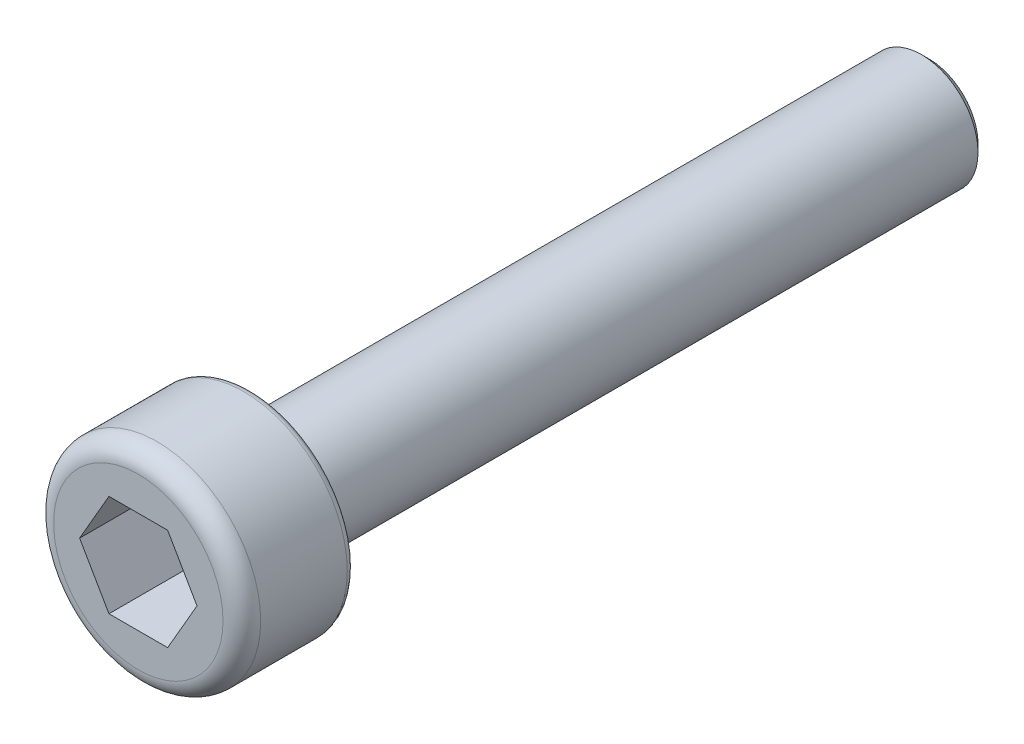
SolidWorks part; units mm, degrees
ref_plane "前视" through (0, 0, 0) normal (0, 0, 1) x (1, 0, 0)
ref_plane "上视" through (0, 0, 0) normal (0, 1, 0) x (1, 0, 0)
ref_plane "右视" through (0, 0, 0) normal (1, 0, 0) x (0, 0, -1)
sketch "草图1" plane through (0, 0, 0) normal (0, 0, 1) x (1, 0, 0)
  circle A0 centre (0, 0) radius 2.75
  dimension "D1" = 5.5
extrude "凸台-拉伸1" add sketch "草图1" along normal blind 3
fillet "圆角1" radius 0.5 1 edges at (2.75, 0, 3)
sketch "草图2" plane through (0, 0, 3) normal (0, 0, 1) x (1, 0, 0)
  line L1 (1.5588, 0) -> (0.7794, 1.35)
  line L2 (0.7794, 1.35) -> (-0.7794, 1.35)
  line L3 (-0.7794, 1.35) -> (-1.5588, 0)
  line L4 (-1.5588, 0) -> (-0.7794, -1.35)
  line L5 (-0.7794, -1.35) -> (0.7794, -1.35)
  line L6 (0.7794, -1.35) -> (1.5588, 0)
  circle A0 centre (0, 0) radius 1.35 construction
  dimension "D1" = 2.7
extrude "切除-拉伸1" cut sketch "草图2" against normal blind 2
sketch "草图3" plane through (0, 0, 0) normal (0, 0, -1) x (-1, 0, 0)
  circle A0 centre (0, 0) radius 1.5
  dimension "D1" = 3
extrude "凸台-拉伸2" add sketch "草图3" along normal blind 18
chamfer "倒角1" distance 0.2 angle 45 1 edges at (-1.5, 0, -18)
fillet "圆角2" radius 0.2 1 edges at (2.75, 0, 0)
